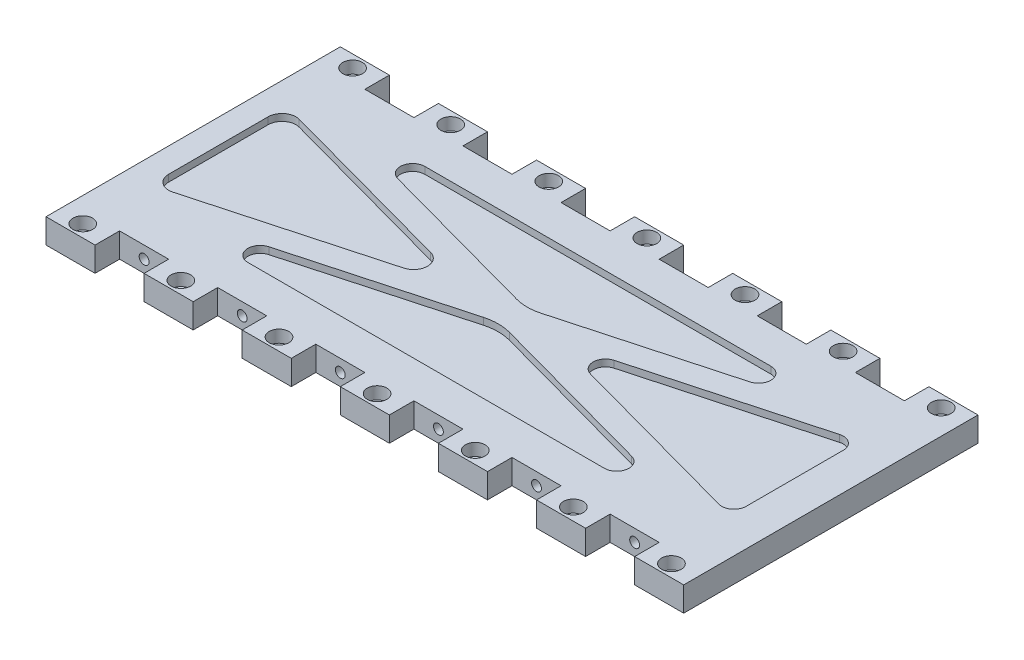
SolidWorks part; units mm, degrees
material "6061-T6 (SS)"
ref_plane "Front Plane" through (0, 0, 0) normal (0, 0, 1) x (1, 0, 0)
ref_plane "Top Plane" through (0, 0, 0) normal (0, 1, 0) x (1, 0, 0)
ref_plane "Right Plane" through (0, 0, 0) normal (1, 0, 0) x (0, 0, -1)
sketch "Sketch1" plane through (0, 0, 0) normal (0, 1, 0) x (1, 0, 0)
  line L1 (165.1, 63.5) -> (-165.1, 63.5)
  line L2 (165.1, 63.5) -> (165.1, -63.5)
  line L3 (165.1, -63.5) -> (-165.1, -63.5)
  line L4 (-165.1, 63.5) -> (-165.1, -63.5)
  line L5 (165.1, 63.5) -> (-165.1, -63.5) construction
  line L6 (165.1, -63.5) -> (-165.1, 63.5) construction
  point P0 (0, 0)
  dimension "D1" = 127
  dimension "D2" = 330.2
extrude "Boss-Extrude1" add sketch "Sketch1" along normal blind 12.7
sketch "Sketch2" plane through (0, 12.7, 0) normal (0, 1, 0) x (1, 0, 0)
  line L0 (165.1, 63.5) -> (-165.1, 63.5) construction
  line L1 (-89.5556, 44.45) -> (89.5556, 44.45)
  line L2 (-152.4, 26.1056) -> (-152.4, -25.3536)
  line L3 (-92.298, -44.45) -> (92.298, -44.45)
  line L4 (146.05, 25.5116) -> (146.05, -24.7597)
  line L5 (-165.1, -63.5) -> (165.1, -63.5) construction
  line L6 (-165.1, 63.5) -> (-165.1, -63.5) construction
  line L7 (165.1, -63.5) -> (165.1, 63.5) construction
  line L8 (-143.2645, 33.0734) -> (-49.4261, 7.3438)
  line L9 (-49.4261, -6.5918) -> (-143.2645, -32.3214)
  line L10 (-91.2347, 31.976) -> (-6.2564, 8.6758)
  line L11 (6.2564, 8.6758) -> (91.2347, 31.976)
  line L12 (138.0209, 31.6356) -> (46.3486, 6.4999)
  line L13 (46.3486, -5.748) -> (138.0209, -30.8837)
  line L14 (93.9771, -31.976) -> (6.7165, -8.05)
  line L15 (-6.7165, -8.05) -> (-93.9771, -31.976)
  line L16 (0, 44.45) -> (0, -44.45) construction
  line L17 (-152.4, 0.376) -> (146.05, 0.376) construction
  arc A0 (138.0209, -30.8837) -> (146.05, -24.7597) centre (139.7, -24.7597) ccw
  arc A1 (46.3486, 6.4999) -> (46.3486, -5.748) centre (48.0277, 0.376) ccw
  arc A2 (138.0209, 31.6356) -> (146.05, 25.5116) centre (139.7, 25.5116) cw
  arc A3 (-91.2347, 31.976) -> (-89.5556, 44.45) centre (-89.5556, 38.1) cw
  arc A4 (91.2347, 31.976) -> (89.5556, 44.45) centre (89.5556, 38.1) ccw
  arc A5 (93.9771, -31.976) -> (92.298, -44.45) centre (92.298, -38.1) cw
  arc A6 (-93.9771, -31.976) -> (-92.298, -44.45) centre (-92.298, -38.1) ccw
  arc A7 (6.7165, -8.05) -> (-6.7165, -8.05) centre (0, -32.5459) ccw
  arc A8 (-6.2564, 8.6758) -> (6.2564, 8.6758) centre (0, 31.4936) ccw
  arc A9 (-49.4261, 7.3438) -> (-49.4261, -6.5918) centre (-51.3366, 0.376) cw
  arc A10 (-143.2645, -32.3214) -> (-152.4, -25.3536) centre (-145.175, -25.3536) cw
  arc A11 (-143.2645, 33.0734) -> (-152.4, 26.1056) centre (-145.175, 26.1056) ccw
  dimension "D5" = 6.35
  dimension "D6" = 12.7
  dimension "D1" = 19.05
  dimension "D2" = 19.05
  dimension "D3" = 12.7
  dimension "D4" = 19.05
  dimension "D7" = 12.7
  dimension "D8" = 12.7
  dimension "D9" = 12.7
  dimension "D10" = 12.7
  dimension "D11" = 12.7
extrude "Cut-Extrude1" cut sketch "Sketch2" against normal blind 3.556
sketch "Sketch3" plane through (0, 0, 0) normal (0, -1, 0) x (1, 0, 0)
  line L0 (-114.3, 76.2) -> (-88.9, 76.2)
  line L1 (-165.1, 63.5) -> (-139.7, 63.5)
  line L2 (-165.1, 63.5) -> (-165.1, 76.2)
  line L3 (-165.1, 76.2) -> (-139.7, 76.2)
  line L4 (-139.7, 63.5) -> (-139.7, 76.2)
  line L5 (-114.3, 63.5) -> (-114.3, 76.2)
  line L6 (-114.3, 63.5) -> (-88.9, 63.5)
  line L7 (-88.9, 63.5) -> (-88.9, 76.2)
  line L8 (-63.5, 76.2) -> (-38.1, 76.2)
  line L9 (-63.5, 63.5) -> (-63.5, 76.2)
  line L10 (-63.5, 63.5) -> (-38.1, 63.5)
  line L11 (-38.1, 63.5) -> (-38.1, 76.2)
  line L12 (-12.7, 76.2) -> (12.7, 76.2)
  line L13 (-12.7, 63.5) -> (-12.7, 76.2)
  line L14 (-12.7, 63.5) -> (12.7, 63.5)
  line L15 (12.7, 63.5) -> (12.7, 76.2)
  line L16 (38.1, 76.2) -> (63.5, 76.2)
  line L17 (38.1, 63.5) -> (38.1, 76.2)
  line L18 (38.1, 63.5) -> (63.5, 63.5)
  line L19 (63.5, 63.5) -> (63.5, 76.2)
  line L20 (88.9, 76.2) -> (114.3, 76.2)
  line L21 (88.9, 63.5) -> (88.9, 76.2)
  line L22 (88.9, 63.5) -> (114.3, 63.5)
  line L23 (114.3, 63.5) -> (114.3, 76.2)
  line L24 (139.7, 76.2) -> (165.1, 76.2)
  line L25 (139.7, 63.5) -> (139.7, 76.2)
  line L26 (139.7, 63.5) -> (165.1, 63.5)
  line L27 (165.1, 63.5) -> (165.1, 76.2)
  line L28 (-114.3, -63.5) -> (-88.9, -63.5)
  line L29 (-114.3, -76.2) -> (-114.3, -63.5)
  line L30 (-114.3, -76.2) -> (-88.9, -76.2)
  line L31 (-88.9, -76.2) -> (-88.9, -63.5)
  line L32 (-63.5, -63.5) -> (-38.1, -63.5)
  line L33 (-63.5, -76.2) -> (-63.5, -63.5)
  line L34 (-63.5, -76.2) -> (-38.1, -76.2)
  line L35 (-38.1, -76.2) -> (-38.1, -63.5)
  line L36 (-12.7, -63.5) -> (12.7, -63.5)
  line L37 (-12.7, -76.2) -> (-12.7, -63.5)
  line L38 (-12.7, -76.2) -> (12.7, -76.2)
  line L39 (12.7, -76.2) -> (12.7, -63.5)
  line L40 (38.1, -63.5) -> (63.5, -63.5)
  line L41 (38.1, -76.2) -> (38.1, -63.5)
  line L42 (38.1, -76.2) -> (63.5, -76.2)
  line L43 (63.5, -76.2) -> (63.5, -63.5)
  line L44 (88.9, -63.5) -> (114.3, -63.5)
  line L45 (88.9, -76.2) -> (88.9, -63.5)
  line L46 (88.9, -76.2) -> (114.3, -76.2)
  line L47 (114.3, -76.2) -> (114.3, -63.5)
  line L48 (139.7, -63.5) -> (165.1, -63.5)
  line L49 (139.7, -76.2) -> (139.7, -63.5)
  line L50 (139.7, -76.2) -> (165.1, -76.2)
  line L51 (165.1, -76.2) -> (165.1, -63.5)
  line L52 (-165.1, -63.5) -> (-139.7, -63.5)
  line L53 (-165.1, -76.2) -> (-165.1, -63.5)
  line L54 (-165.1, -76.2) -> (-139.7, -76.2)
  line L55 (-139.7, -76.2) -> (-139.7, -63.5)
  dimension "D1" = 12.7
  dimension "D2" = 25.4
  dimension "D3" = 7
  dimension "D4" = 2
extrude "Boss-Extrude2" add sketch "Sketch3" against normal blind 12.7
sketch "Sketch4" plane through (0, 12.7, 0) normal (0, 1, 0) x (1, 0, 0)
  line L0 (-165.1, 76.2) -> (-139.7, 63.5) construction
  circle A0 centre (-152.4, 69.85) radius 3.2385
  circle A1 centre (-101.6, 69.85) radius 3.2385
  circle A2 centre (-50.8, 69.85) radius 3.2385
  circle A3 centre (0, 69.85) radius 3.2385
  circle A4 centre (50.8, 69.85) radius 3.2385
  circle A5 centre (101.6, 69.85) radius 3.2385
  circle A6 centre (152.4, 69.85) radius 3.2385
  circle A7 centre (-101.6, -69.85) radius 3.2385
  circle A8 centre (-50.8, -69.85) radius 3.2385
  circle A9 centre (0, -69.85) radius 3.2385
  circle A10 centre (50.8, -69.85) radius 3.2385
  circle A11 centre (101.6, -69.85) radius 3.2385
  circle A12 centre (152.4, -69.85) radius 3.2385
  circle A13 centre (-152.4, -69.85) radius 3.2385
  dimension "D1" = 6.477
  dimension "D2" = 7
  dimension "D3" = 2
extrude "Cut-Extrude2" cut sketch "Sketch4" against normal blind 25.4
sketch "Sketch5" plane through (0, 12.7, 0) normal (0, 1, 0) x (1, 0, 0)
  circle A0 centre (-152.4, 69.85) radius 5.08
  circle A1 centre (-101.6, 69.85) radius 5.08
  circle A2 centre (-50.8, 69.85) radius 5.08
  circle A3 centre (0, 69.85) radius 5.08
  circle A4 centre (50.8, 69.85) radius 5.08
  circle A5 centre (101.6, 69.85) radius 5.08
  circle A6 centre (152.4, 69.85) radius 5.08
  circle A7 centre (-101.6, -69.85) radius 5.08
  circle A8 centre (-50.8, -69.85) radius 5.08
  circle A9 centre (0, -69.85) radius 5.08
  circle A10 centre (50.8, -69.85) radius 5.08
  circle A11 centre (101.6, -69.85) radius 5.08
  circle A12 centre (152.4, -69.85) radius 5.08
  circle A13 centre (-152.4, -69.85) radius 5.08
  dimension "D1" = 10.16
  dimension "D2" = 7
  dimension "D3" = 2
extrude "Cut-Extrude3" cut sketch "Sketch5" against normal blind 6.35
sketch "Sketch6" plane through (0, 0, 63.5) normal (0, 0, 1) x (1, 0, 0)
  line L0 (-139.7, 12.7) -> (-114.3, 0) construction
  circle A0 centre (-127, 6.35) radius 2.5527
  circle A1 centre (-76.2, 6.35) radius 2.5527
  circle A2 centre (-25.4, 6.35) radius 2.5527
  circle A3 centre (25.4, 6.35) radius 2.5527
  circle A4 centre (76.2, 6.35) radius 2.5527
  circle A5 centre (127, 6.35) radius 2.5527
  dimension "D1" = 5.1054
  dimension "D2" = 6
extrude "Cut-Extrude4" cut sketch "Sketch6" against normal blind 25.4
ref_plane "Plane1" through (0, 6.35, 0) normal (0, 1, 0) x (1, 0, 0)
ref_plane "Plane2" through (0, 0, 0) normal (0, 0, -1) x (1, 0, 0)
mirror "Mirror1" about plane through (0, 0, 0) normal (0, 0, -1) of "Cut-Extrude4"
mirror "Mirror2" about plane through (0, 6.35, 0) normal (0, 1, 0) of "Cut-Extrude1"
